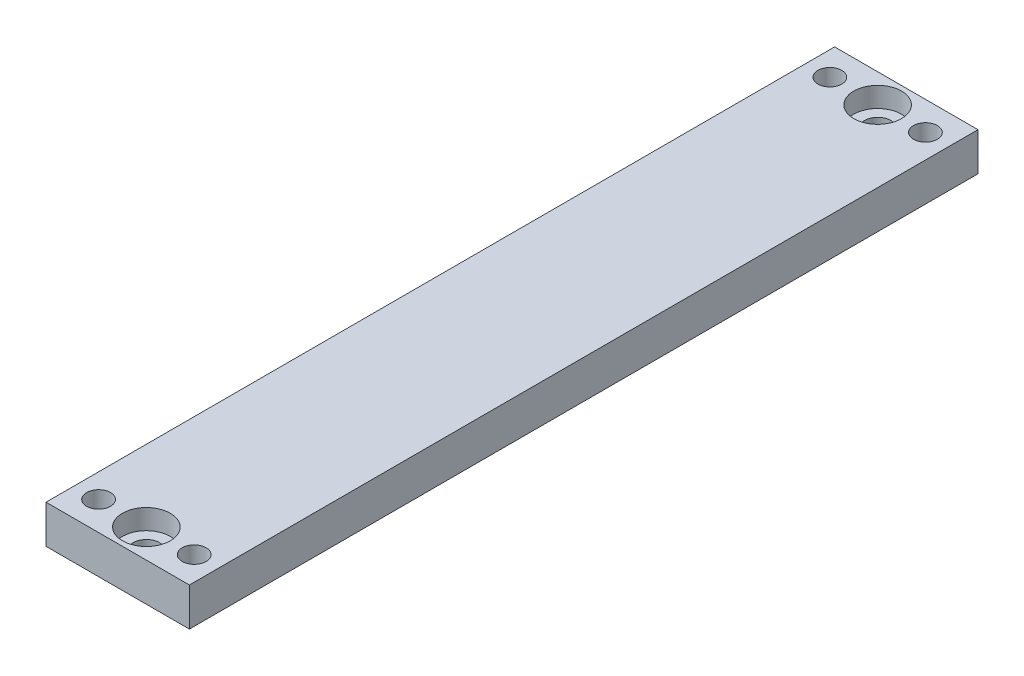
SolidWorks part; units mm, degrees
ref_plane "Front Plane" through (0, 0, 0) normal (0, 0, 1) x (1, 0, 0)
ref_plane "Top Plane" through (0, 0, 0) normal (0, 1, 0) x (1, 0, 0)
ref_plane "Right Plane" through (0, 0, 0) normal (1, 0, 0) x (0, 0, -1)
sketch "Sketch2" plane through (0, 0, 0) normal (0, 1, 0) x (1, 0, 0)
  line L1 (-15, 82.5) -> (15, 82.5)
  line L2 (-15, 82.5) -> (-15, -82.5)
  line L3 (-15, -82.5) -> (15, -82.5)
  line L4 (15, 82.5) -> (15, -82.5)
  line L5 (-15, 82.5) -> (15, -82.5) construction
  line L6 (-15, -82.5) -> (15, 82.5) construction
  point P0 (0, 0)
  dimension "D1" = 165
  dimension "D2" = 30
extrude "Boss-Extrude1" add sketch "Sketch2" along normal blind 8
sketch "Sketch3" plane through (0, 8, 0) normal (0, 1, 0) x (1, 0, 0)
  line L0 (-15, -82.5) -> (15, -82.5) construction
  line L1 (15, 82.5) -> (-15, 82.5) construction
  circle A0 centre (0, -76.5) radius 2.75
  circle A1 centre (0, 76.5) radius 2.75
  dimension "D1" = 6
  dimension "D2" = 6
extrude "Cut-Extrude1" cut sketch "Sketch3" against normal blind 8
sketch "Sketch4" plane through (0, 8, 0) normal (0, 1, 0) x (1, 0, 0)
  circle A0 centre (0, 76.5) radius 5
  circle A1 centre (0, -76.5) radius 5
extrude "Cut-Extrude2" cut sketch "Sketch4" against normal blind 4.2
sketch "Sketch5" plane through (0, 8, 0) normal (0, 1, 0) x (1, 0, 0)
  line L0 (-15, -82.5) -> (15, -82.5) construction
  line L1 (-15, 82.5) -> (-15, -82.5) construction
  line L2 (15, -82.5) -> (15, 82.5) construction
  line L3 (15, 82.5) -> (-15, 82.5) construction
  circle A0 centre (-10, 76.5) radius 2.5
  circle A1 centre (10, 76.5) radius 2.5
  circle A2 centre (-10, -76.5) radius 2.5
  circle A3 centre (10, -76.5) radius 2.5
  dimension "D1" = 6
  dimension "D2" = 6
  dimension "D3" = 5
  dimension "D4" = 5
  dimension "D5" = 5
  dimension "D6" = 5
  dimension "D7" = 6
  dimension "D8" = 6
extrude "Cut-Extrude3" cut sketch "Sketch5" against normal blind 41.2
